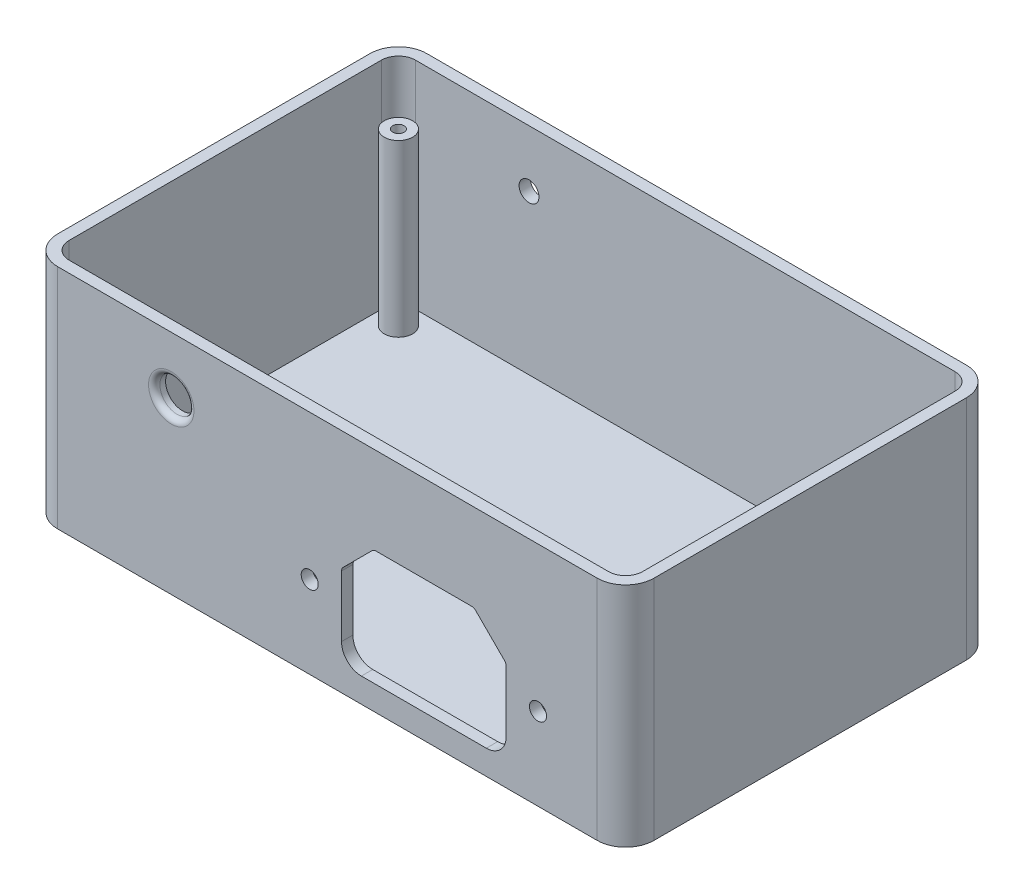
SolidWorks part; units mm, degrees
material "Nylon 101"
ref_plane "Front Plane" through (0, 0, 0) normal (0, 0, 1) x (1, 0, 0)
ref_plane "Top Plane" through (0, 0, 0) normal (0, 1, 0) x (1, 0, 0)
ref_plane "Right Plane" through (0, 0, 0) normal (1, 0, 0) x (0, 0, -1)
sketch "Sketch1" plane through (0, 0, 0) normal (0, 1, 0) x (1, 0, 0)
  line L0 (0, 0) -> (0, 65)
  line L1 (0, 65) -> (105, 65)
  line L2 (105, 65) -> (105, 0)
  line L3 (105, 0) -> (0, 0)
  dimension "D1" = 105
  dimension "D2" = 65
extrude "Boss-Extrude1" add sketch "Sketch1" along normal blind 40
fillet "Fillet1" radius 5 4 edges at (0, 20, -65) (105, 20, -65) (105, 20, 0) (0, 20, 0)
sketch "Sketch3" plane through (0, 40, 0) normal (0, 1, 0) x (1, 0, 0)
  line L12 (100, 63) -> (5, 63)
  line L13 (2, 60) -> (2, 5)
  line L14 (5, 2) -> (100, 2)
  line L15 (103, 5) -> (103, 60)
  line L16 (100, 63) -> (5, 63)
  line L17 (2, 60) -> (2, 5)
  line L18 (5, 2) -> (100, 2)
  line L19 (103, 5) -> (103, 60)
  arc A12 (5, 63) -> (2, 60) centre (5, 60) ccw
  arc A13 (2, 5) -> (5, 2) centre (5, 5) ccw
  arc A14 (100, 2) -> (103, 5) centre (100, 5) ccw
  arc A15 (103, 60) -> (100, 63) centre (100, 60) ccw
  arc A16 (5, 63) -> (2, 60) centre (5, 60) ccw
  arc A17 (2, 5) -> (5, 2) centre (5, 5) ccw
  arc A18 (100, 2) -> (103, 5) centre (100, 5) ccw
  arc A19 (103, 60) -> (100, 63) centre (100, 60) ccw
  dimension "D1" = 2
extrude "Cut-Extrude1" cut sketch "Sketch3" against normal blind 38
sketch "Sketch4" plane through (0, 2, 0) normal (0, 1, 0) x (1, 0, 0)
  line L0 (5, 2) -> (100, 2) construction
  line L1 (103, 5) -> (103, 60) construction
  circle A0 centre (99, 6) radius 2.5
  circle A1 centre (99, 6) radius 1
  dimension "D1" = 5
  dimension "D2" = 2
  dimension "D3" = 4
  dimension "D4" = 4
extrude "Boss-Extrude2" add sketch "Sketch4" along normal blind 30 contours A1 | A0
ref_plane "Plane1" through (52.5, 0, 0) normal (-1, 0, 0) x (0, 0, 1)
ref_plane "Plane2" through (0, 0, -32.5) normal (0, 0, -1) x (-1, 0, 0)
mirror "Mirror1" about plane through (0, 0, -32.5) normal (0, 0, -1) of "Boss-Extrude2"
mirror "Mirror2" about plane through (52.5, 0, 0) normal (-1, 0, 0) of "Mirror1", "Boss-Extrude2"
sketch "Sketch7" plane through (0, 0, 0) normal (0, 0, 1) x (1, 0, 0)
  line L30 (83.6837, 19.2801) -> (78.5979, 24.3659)
  line L31 (83.9766, 7.8087) -> (83.9766, 18.573)
  line L32 (58.4766, 4.3087) -> (80.4766, 4.3087)
  line L33 (54.9766, 18.573) -> (54.9766, 7.8087)
  line L34 (60.3553, 24.3659) -> (55.2695, 19.2801)
  line L35 (77.8908, 24.6587) -> (61.0624, 24.6587)
  line L36 (83.6837, 19.2801) -> (78.5979, 24.3659)
  line L37 (83.9766, 7.8087) -> (83.9766, 18.573)
  line L38 (58.4766, 4.3087) -> (80.4766, 4.3087)
  line L39 (54.9766, 18.573) -> (54.9766, 7.8087)
  line L40 (60.3553, 24.3659) -> (55.2695, 19.2801)
  line L41 (77.8908, 24.6587) -> (61.0624, 24.6587)
  arc A30 (83.9766, 18.573) -> (83.6837, 19.2801) centre (82.9766, 18.573) ccw
  arc A31 (80.4766, 4.3087) -> (83.9766, 7.8087) centre (80.4766, 7.8087) ccw
  arc A32 (54.9766, 7.8087) -> (58.4766, 4.3087) centre (58.4766, 7.8087) ccw
  arc A33 (55.2695, 19.2801) -> (54.9766, 18.573) centre (55.9766, 18.573) ccw
  arc A34 (61.0624, 24.6587) -> (60.3553, 24.3659) centre (61.0624, 23.6587) ccw
  arc A35 (78.5979, 24.3659) -> (77.8908, 24.6587) centre (77.8908, 23.6587) ccw
  arc A36 (83.9766, 18.573) -> (83.6837, 19.2801) centre (82.9766, 18.573) ccw
  arc A37 (80.4766, 4.3087) -> (83.9766, 7.8087) centre (80.4766, 7.8087) ccw
  arc A38 (54.9766, 7.8087) -> (58.4766, 4.3087) centre (58.4766, 7.8087) ccw
  arc A39 (55.2695, 19.2801) -> (54.9766, 18.573) centre (55.9766, 18.573) ccw
  arc A40 (61.0624, 24.6587) -> (60.3553, 24.3659) centre (61.0624, 23.6587) ccw
  arc A41 (78.5979, 24.3659) -> (77.8908, 24.6587) centre (77.8908, 23.6587) ccw
  circle A74 centre (89.5766, 14.4837) radius 1.5
  circle A75 centre (89.5766, 14.4837) radius 1.5
  circle A78 centre (49.3766, 14.4837) radius 1.5
  circle A79 centre (49.3766, 14.4837) radius 1.5
  dimension "D1" = 0.5
  dimension "D2" = 1
  dimension "D3" = 1
extrude "Cut-Extrude2" cut sketch "Sketch7" against normal up to next
sketch "Sketch9" plane through (0, 2, 0) normal (0, 1, 0) x (1, 0, 0)
  line L0 (20.9, 32.5) -> (-20.9, 32.5) construction
  line L1 (103, 5) -> (103, 60) construction
  line L2 (52.5, 20.9) -> (52.5, -20.9) construction
  circle A0 centre (93, 32.5) radius 2
  circle A1 centre (12, 32.5) radius 2
  dimension "D1" = 4
  dimension "D2" = 10
extrude "Cut-Extrude3" cut sketch "Sketch9" against normal up to next
sketch "Sketch12" plane through (0, 0, 0) normal (0, 0, 1) x (1, 0, 0)
  line L0 (5, 40) -> (5, 0) construction
  line L1 (5, 40) -> (100, 40) construction
  circle A0 centre (25, 30) radius 3
  dimension "D1" = 6
  dimension "D2" = 20
  dimension "D3" = 10
extrude "Cut-Extrude4" cut sketch "Sketch12" against normal up to next
fillet "Fillet2" radius 1 1 edges at (28, 30, 0)
sketch "Sketch13" plane through (0, 0, -65) normal (0, 0, -1) x (-1, 0, 0)
  line L0 (-100, 40) -> (-5, 40) construction
  line L1 (-5, 0) -> (-5, 40) construction
  circle A0 centre (-25, 30) radius 1.75
  dimension "D1" = 3.5
  dimension "D2" = 10
  dimension "D3" = 20
extrude "Cut-Extrude5" cut sketch "Sketch13" against normal up to next
